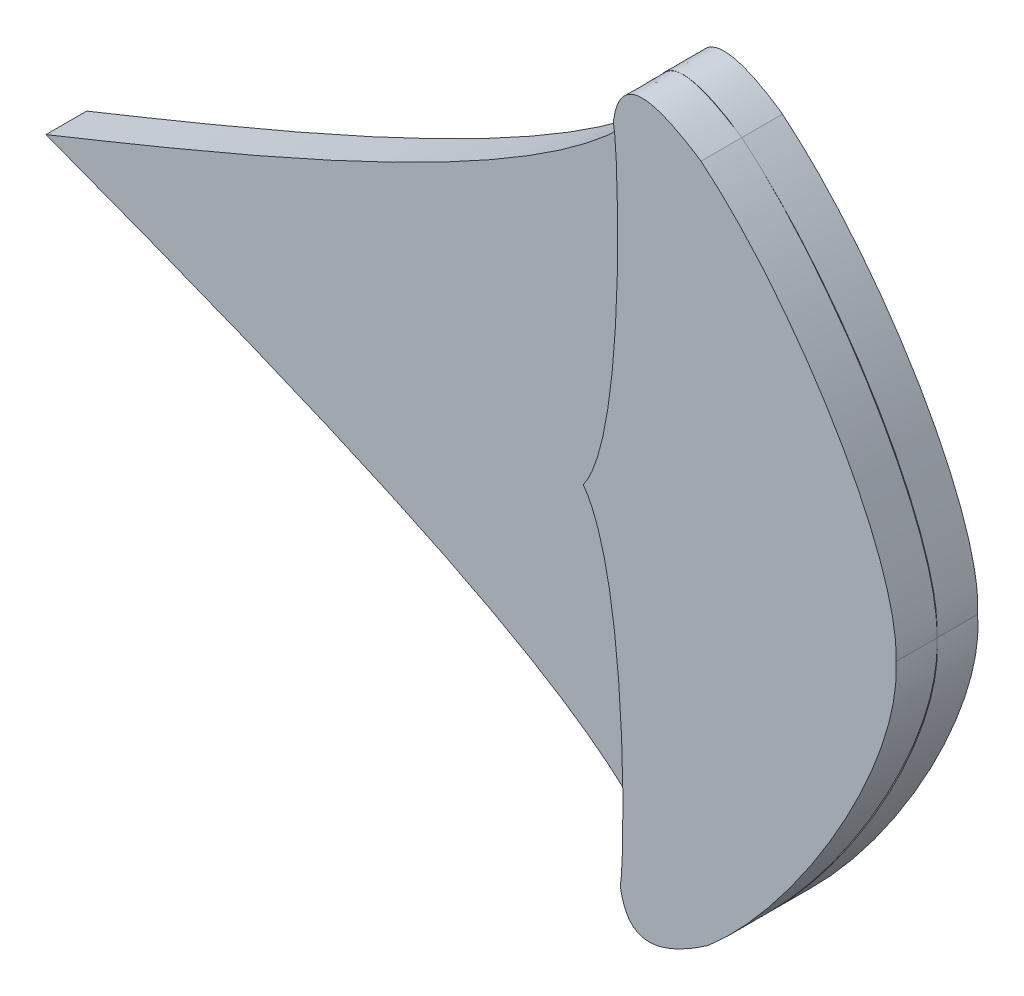
SolidWorks part; units mm, degrees
ref_plane "Front Plane" through (0, 0, 0) normal (0, 0, 1) x (1, 0, 0)
ref_plane "Top Plane" through (0, 0, 0) normal (0, 1, 0) x (1, 0, 0)
ref_plane "Right Plane" through (0, 0, 0) normal (1, 0, 0) x (0, 0, -1)
sketch "Sketch3" plane through (0, 0, 0) normal (0, 0, 1) x (1, 0, 0)
  line L0 (318.6667, 759.5) -> (1593.3333, 759.5) construction
  line L1 (113.6824, 746.2529) -> (1788.3167, 763.9634) construction
  spline S0 degree 3 poles (1191.0347, 757.6467) (1192.5016, 777.2786) (1169.1524, 818.534) (1143.162, 840.0686) knots 0 0 0 0 1 1 1 1
  spline S1 degree 3 poles (1143.162, 840.0686) (1137.2749, 844.2456) (1123.107, 852.7886) (1121.635, 837.7155) knots 0 0 0 0 1 1 1 1
  spline S2 degree 3 poles (1121.635, 837.7155) (1107.85, 810.7804) (1034.1811, 780.1625) (972.4008, 755.3345) knots 0 0 0 0 1 1 1 1
  spline S4 degree 3 poles (1191.0347, 757.6467) (1192.9165, 738.0502) (1170.445, 696.3102) (1144.9159, 674.2308) knots 0 0 0 0 1 1 1 1
  spline S5 degree 3 poles (1144.9159, 674.2308) (1139.1184, 669.9302) (1125.1344, 661.0895) (1123.3439, 676.1281) knots 0 0 0 0 1 1 1 1
  spline S6 degree 3 poles (1123.3439, 676.1281) (1108.9923, 702.7656) (1034.6924, 731.8187) (972.4008, 755.3345) knots 0 0 0 0 1 1 1 1
extrude "Boss-Extrude1" add sketch "Sketch3" along normal blind 10
sketch "Sketch4" plane through (0, 0, 10) normal (0, 0, 1) x (1, 0, 0)
  line L0 (972.4008, 755.3345) -> (1191.0347, 757.6467) construction
  spline S0 degree 3 poles (1121.635, 837.7155) (1122.9943, 832.1824) (1124.9694, 771.6854) (1114.2662, 756.8348) knots 0 0 0 0 1 1 1 1
  spline S3 degree 3 poles (1123.3439, 676.1281) (1124.5859, 681.6887) (1125.2811, 742.2139) (1114.2662, 756.8348) knots 0 0 0 0 1 1 1 1
  spline S8 degree 3 poles (1121.635, 837.7155) (1123.1315, 848.7206) (1130.202, 848.6176) (1143.162, 840.0686) knots 0 0 0 0 1 1 1 1
  spline S9 degree 3 poles (1143.162, 840.0686) (1166.1273, 821.2452) (1191.8973, 779.5926) (1191.0347, 757.6467) knots 0 0 0 0 1 1 1 1
  spline S10 degree 3 poles (1123.3439, 676.1281) (1125.0728, 665.1571) (1132.1395, 665.4096) (1144.9159, 674.2308) knots 0 0 0 0 1 1 1 1
  spline S11 degree 3 poles (1144.9159, 674.2308) (1167.478, 693.5357) (1192.3613, 735.724) (1191.0347, 757.6467) knots 0 0 0 0 1 1 1 1
extrude "Boss-Extrude2" add sketch "Sketch4" along normal blind 10 contours S0 S3 S10 S11 S9 S8
